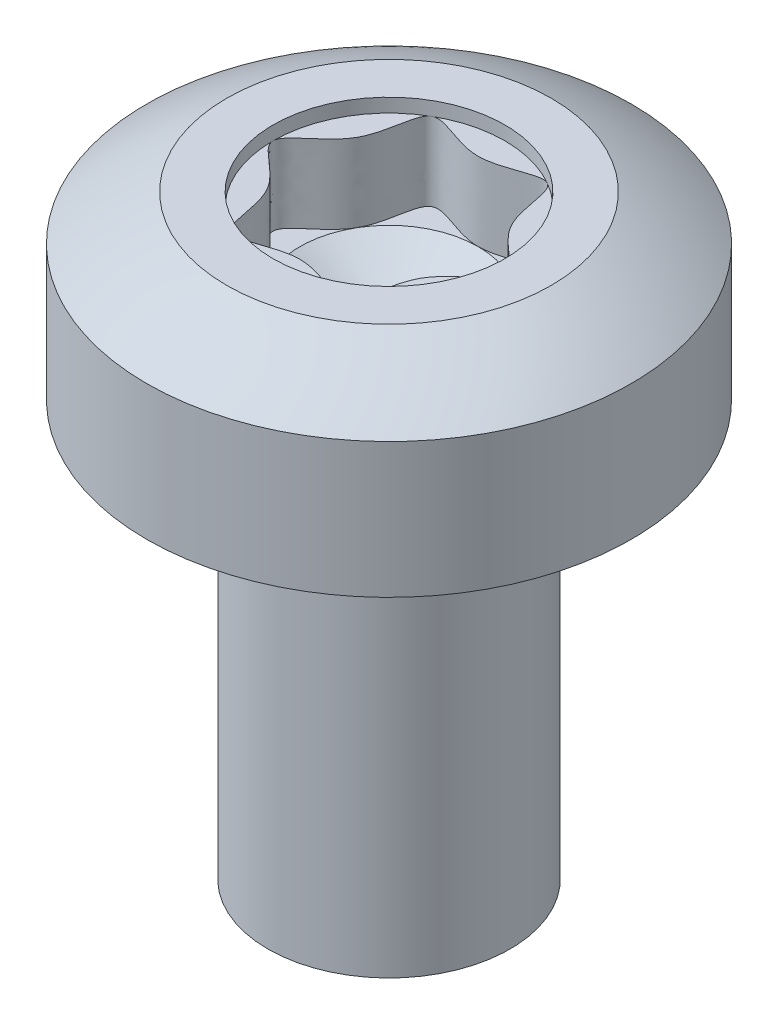
SolidWorks part; units mm, degrees
material "AISI 316L Acero inoxidable"
ref_plane "Front" through (0, 0, 0) normal (0, 0, 1) x (1, 0, 0)
ref_plane "Top" through (0, 0, 0) normal (0, 1, 0) x (1, 0, 0)
ref_plane "Right" through (0, 0, 0) normal (1, 0, 0) x (0, 0, -1)
sketch "Sketch1" plane through (0, 0, 0) normal (0, 0, 1) x (1, 0, 0)
  line L0 (0, 0) -> (0, 34.6184) construction
  line L1 (0, 0) -> (1.75, 0)
  line L2 (1.75, 0) -> (1.75, 6)
  line L3 (1.75, 6) -> (3.5, 6)
  line L4 (3.5, 6) -> (3.5, 8.6)
  line L5 (3.5, 8.6) -> (0, 8.6)
  line L6 (0, 8.6) -> (0, 0)
  line L7 (3.5, 6) -> (4.1, 6) construction
  line L8 (4.1, 6) -> (4.1, 1.2) construction
  dimension "HEAD_DIA" = 7
  dimension "HEAD_HT" = 2.6
  dimension "LENGTH" = 6
  dimension "DIA" = 3.5
  dimension "pitch" = 0.6
  dimension "thread_length" = 4.8
revolve "BODY" add sketch "Sketch1" angle 360 about L0
cosmetic thread "ThreadCosmetic" [suppressed] parameters "D1"=4.8, "D2"=2.8505
sketch "Sketch2" plane through (0, 0, 0) normal (0, 0, 1) x (1, 0, 0)
  line L0 (3.5, 7.95) -> (0, 3.0766) construction
  line L3 (3.5, 6) -> (3.5, 8.6) construction
  line L4 (0, 0) -> (0, 34.6184) construction
  line L5 (0, 9.0766) -> (0, 9.5588)
  line L6 (6, 3.0766) -> (6, 9.5588)
  line L7 (6, 9.5588) -> (0, 9.5588)
  line L8 (0, 9.5588) -> (6, 9.5588)
  arc A0 (6, 3.0766) -> (0, 9.0766) centre (0, 3.0766) ccw
  dimension "SPHERE_DIA" = 6
  dimension "D1" = 0.65
  dimension "D2" = 0.4822
revolve "HEAD-CUT" cut sketch "Sketch2" angle 360 about axis through (0, 0, 0) along (0, 1, 0)
sketch "Sketch4" plane through (0, 0, 0) normal (0, 0, 1) x (1, 0, 0)
  line L0 (-1.75, 4.8) -> (-1.6842, 5.9)
  line L1 (-1.75, 6) -> (-1.75, 0) construction
  line L2 (-1.75, 6) -> (-1.75, 4.8)
  arc A0 (-1.6842, 5.9) -> (-1.75, 6) centre (-1.784, 5.906) ccw
  dimension "CONER_RAD" = 0.1
  dimension "D1" = 0.1
  dimension "GAP" = 1.2
revolve "GAP" cut sketch "Sketch4" angle 360 about axis through (0, 0, 0) along (0, 1, 0)
sketch "Sketch5" plane through (0, 8.6, 0) normal (0, 1, 0) x (-1, 0, 0)
  line L0 (0, 1.2885) -> (0, 0) construction
  line L1 (0, 0) -> (0.8375, 1.4506) construction
  line L2 (0.8375, 1.4506) -> (-0.8375, 1.4506) construction
  line L3 (-0.8375, 1.4506) -> (-1.675, 0) construction
  line L4 (-1.675, 0) -> (-0.8375, -1.4506) construction
  line L5 (-0.8375, -1.4506) -> (0.8375, -1.4506) construction
  line L6 (0.8375, -1.4506) -> (1.675, 0) construction
  line L7 (1.675, 0) -> (0.8375, 1.4506) construction
  line L8 (0, 1.2885) -> (-1.1158, 0.6442) construction
  line L9 (-1.1158, 0.6442) -> (-1.1158, -0.6442) construction
  line L10 (-1.1158, -0.6442) -> (0, -1.2885) construction
  line L11 (0, -1.2885) -> (1.1158, -0.6442) construction
  line L12 (1.1158, -0.6442) -> (1.1158, 0.6442) construction
  line L13 (1.1158, 0.6442) -> (0, 1.2885) construction
  circle A0 centre (0, 0) radius 1.2885 construction
  circle A1 centre (0, 0) radius 1.675
  spline S0 degree 3 poles (1.0312, 1.786) (0, 1.0397) (-1.0312, 1.786) (-0.9004, 0.5198) (-2.0623, 0) (-0.9004, -0.5198) (-1.0312, -1.786) (0, -1.0397) (1.0312, -1.786) (0.9004, -0.5198) (2.0623, 0) (0.9004, 0.5198) (1.0312, 1.786) (0, 1.0397) (-1.0312, 1.786) knots -0.25 -0.166667 -0.083333 0 0.083333 0.166667 0.25 0.333333 0.416667 0.5 0.583333 0.666667 0.75 0.833333 0.916667 1 1.083333 1.166667 1.25 only from (0, 1.2885) to (0, 1.2885)
  dimension "slot_dia" = 3.35
  dimension "D3" = 2.5769
  dimension "D1" = 30
extrude "Recess-Cut-Extrude1" cut sketch "Sketch5" against normal blind 1.33
sketch "Sketch3" plane through (0, 0, 0) normal (0, 0, 1) x (1, 0, 0)
  line L0 (0, 6.5261) -> (1.2885, 7.27)
  line L1 (0, 0) -> (0, 34.6184) construction
  line L2 (1.2885, 7.27) -> (0, 7.27)
  line L3 (0, 7.27) -> (0, 6.5261)
  dimension "D1" = 60
  dimension "DRILL_RAD" = 1.2885
  dimension "SLOT_DEP" = 1.33
revolve "DRILL-CUT" cut sketch "Sketch3" angle 360 about axis through (0, 0, 0) along (0, 1, 0)
sketch "Sketch6" plane through (0, 0, 0) normal (0, 0, 1) x (1, 0, 0)
  line L0 (1.75, 0) -> (1.4252, 0.1875)
  line L1 (1.4252, 0.1875) -> (1.75, 0.375)
  line L4 (1.75, 0.375) -> (1.75, 0)
  line L5 (0, 0) -> (0, 34.6184) construction
  dimension "D1" = 1.4252
revolve "ThreadSchematic" [suppressed] cut sketch "Sketch6" angle 360 about axis through (0, 0, 0) along (0, 1, 0)
pattern_linear "ThdSchPat" [suppressed] count 8 spacing 0.6 along (0, 1, 0)
sketch "Sketch7" plane through (0, 8.6, 0) normal (0, 1, 0) x (-1, 0, 0)
  circle A0 centre (0, 0) radius 1.675
  dimension "D1" = 3.35
extrude "Recess-Cut-Extrude2" cut sketch "Sketch7" against normal blind 0.1995
equation "\"D1@Sketch2\" = \"HEAD_HT@Sketch1\" * 0.25"
equation "\"D1@Sketch4\" = \"CONER_RAD@Sketch4\""
equation "\"D1@Recess-Cut-Extrude1\" = \"SLOT_DEP@Sketch3\""
equation "\"D1@Sketch7\" = \"slot_dia@Sketch5\""
equation "\"D1@Recess-Cut-Extrude2\" = \"SLOT_DEP@Sketch3\" * 0.15"
equation "\"D3@Sketch5\" = \"slot_dia@Sketch5\" / 1.3"
equation "\"DRILL_RAD@Sketch3\" = \"D3@Sketch5\" * 0.5"
equation "\"D1@ThreadCosmetic\" = \"thread_length@Sketch1\""
equation "\"D2@ThreadCosmetic\" = \"DIA@Sketch1\" - 1.0825 * \"pitch@Sketch1\""
equation "\"D1@Sketch6\" = \"D2@ThreadCosmetic\" / 2"
equation "\"D3@ThdSchPat\" = \"pitch@Sketch1\""
equation "\"D1@ThdSchPat\" = \"thread_length@Sketch1\" / \"pitch@Sketch1\""
